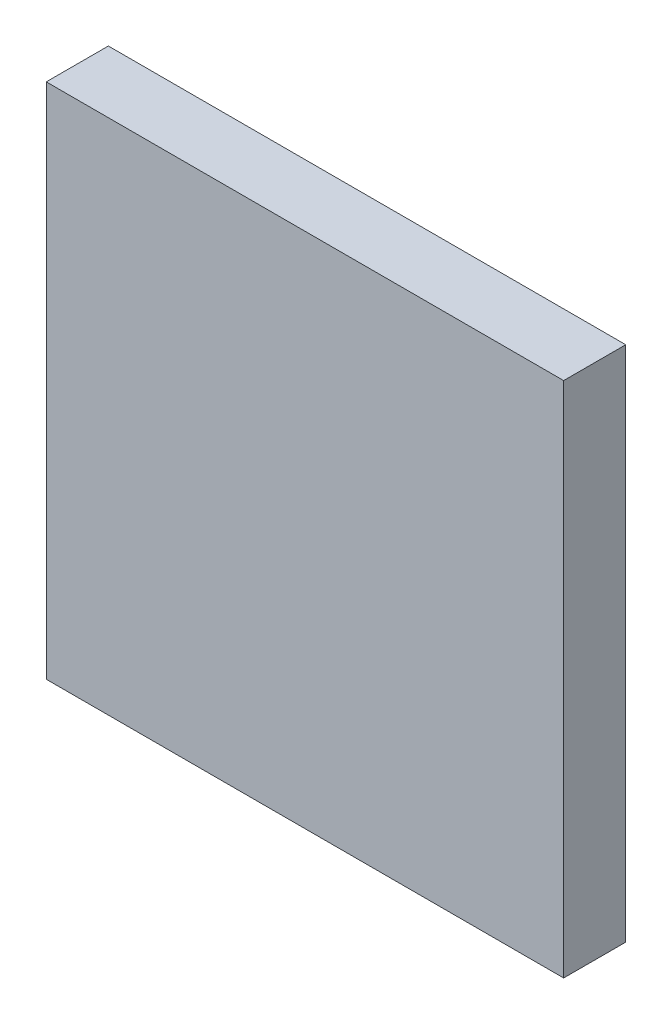
SolidWorks part; units mm, degrees
ref_plane "Front Plane" through (0, 0, 0) normal (0, 0, 1) x (1, 0, 0)
ref_plane "Top Plane" through (0, 0, 0) normal (0, 1, 0) x (1, 0, 0)
ref_plane "Right Plane" through (0, 0, 0) normal (1, 0, 0) x (0, 0, -1)
sketch "Sketch1" plane through (0, 0, 0) normal (0, 0, 1) x (1, 0, 0)
  line L1 (-21.3443, 29.0684) -> (28.6557, 29.0684)
  line L2 (-21.3443, 29.0684) -> (-21.3443, -20.9316)
  line L3 (-21.3443, -20.9316) -> (28.6557, -20.9316)
  line L4 (28.6557, 29.0684) -> (28.6557, -20.9316)
  dimension "D1" = 50
  dimension "D2" = 50
extrude "Boss-Extrude1" add sketch "Sketch1" along normal blind 6
